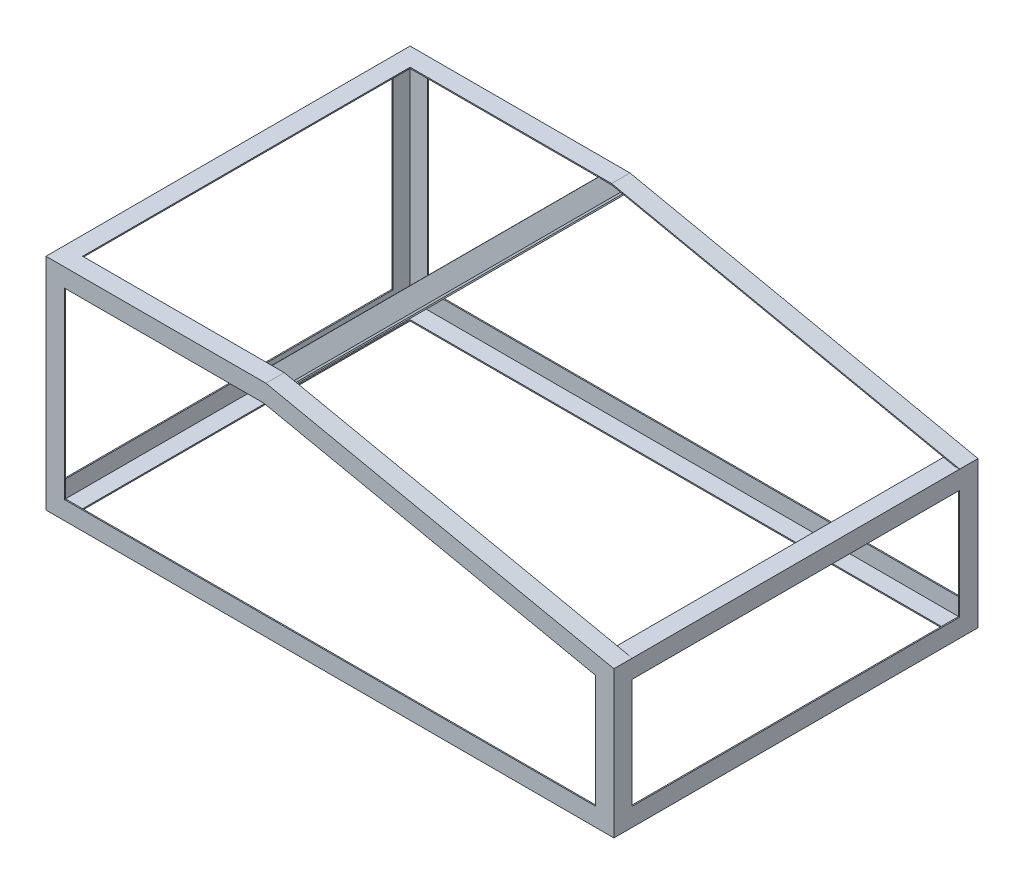
SolidWorks part; units mm, degrees
material "6061 Alloy"
ref_plane "Front Plane" through (0, 0, 0) normal (0, 0, 1) x (1, 0, 0)
ref_plane "Top Plane" through (0, 0, 0) normal (0, 1, 0) x (1, 0, 0)
ref_plane "Right Plane" through (0, 0, 0) normal (1, 0, 0) x (0, 0, -1)
sketch "Sketch2" plane through (0, 0, 0) normal (1, 0, 0) x (0, 0, -1)
  line L0 (-504.825, -346.075) -> (-504.825, -422.275)
  line L1 (504.825, -422.275) -> (-504.825, -422.275) construction
  line L2 (504.825, -422.275) -> (504.825, 422.275) construction
  line L3 (504.825, 422.275) -> (-504.825, 422.275) construction
  line L4 (-504.825, -422.275) -> (-504.825, 422.275) construction
  line L5 (504.825, -422.275) -> (-504.825, 422.275) construction
  line L6 (504.825, 422.275) -> (-504.825, -422.275) construction
  line L7 (-504.825, -422.275) -> (-428.625, -422.275)
  line L8 (-428.625, -422.275) -> (-428.625, -417.195)
  line L9 (-428.625, -417.195) -> (-498.7519, -417.195)
  line L10 (-498.7519, -417.195) -> (-498.7519, -346.075)
  line L11 (-498.7519, -346.075) -> (-504.825, -346.075)
  line L12 (0, 0) -> (0, -148.4726) construction
  line L13 (0, 0) -> (158.633, 0) construction
  line L14 (498.7519, -417.195) -> (498.7519, -346.075)
  line L15 (428.625, -417.195) -> (498.7519, -417.195)
  line L16 (428.625, -422.275) -> (428.625, -417.195)
  line L17 (504.825, -422.275) -> (428.625, -422.275)
  line L18 (504.825, -346.075) -> (504.825, -422.275)
  line L19 (498.7519, -346.075) -> (504.825, -346.075)
  line L20 (428.625, 417.195) -> (498.7519, 417.195)
  line L21 (428.625, 422.275) -> (428.625, 417.195)
  line L22 (504.825, 422.275) -> (428.625, 422.275)
  line L23 (504.825, 346.075) -> (504.825, 422.275)
  line L24 (498.7519, 346.075) -> (504.825, 346.075)
  line L25 (498.7519, 417.195) -> (498.7519, 346.075)
  line L26 (-498.7519, 417.195) -> (-498.7519, 346.075)
  line L27 (-428.625, 417.195) -> (-498.7519, 417.195)
  line L28 (-428.625, 422.275) -> (-428.625, 417.195)
  line L29 (-504.825, 422.275) -> (-428.625, 422.275)
  line L30 (-504.825, 346.075) -> (-504.825, 422.275)
  line L31 (-498.7519, 346.075) -> (-504.825, 346.075)
  point P0 (0, 0)
  dimension "D1" = 1009.65
  dimension "D2" = 844.55
  dimension "D3" = 76.2
  dimension "D4" = 5.08
extrude "OAL Lenth" [suppressed] add sketch "Sketch2" along normal blind 1574.8
sketch "Sketch3" [suppressed] plane through (0, 0, 0) normal (0, 0, 1) x (1, 0, 0)
  line L0 (0, -422.275) -> (0, -346.075)
  line L1 (1574.8, -346.075) -> (0, -346.075) construction
  line L2 (0, -346.075) -> (0, -422.275) construction
  line L3 (0, -346.075) -> (5.08, -346.075)
  line L4 (5.08, -346.075) -> (5.08, -417.195)
  line L5 (5.08, -417.195) -> (76.2, -417.195)
  line L6 (76.2, -417.195) -> (76.2, -422.275)
  line L7 (1574.8, -422.275) -> (0, -422.275) construction
  line L8 (76.2, -422.275) -> (0, -422.275)
  line L9 (0, 0) -> (697.1877, 0) construction
  line L10 (787.4, 346.075) -> (787.4, -346.075) construction
  line L11 (1574.8, 346.075) -> (0, 346.075) construction
  line L12 (76.2, 422.275) -> (0, 422.275)
  line L13 (76.2, 417.195) -> (76.2, 422.275)
  line L14 (5.08, 417.195) -> (76.2, 417.195)
  line L15 (5.08, 346.075) -> (5.08, 417.195)
  line L16 (0, 346.075) -> (5.08, 346.075)
  line L17 (0, 422.275) -> (0, 346.075)
  line L18 (1574.8, 422.275) -> (1574.8, 346.075)
  line L19 (1574.8, 346.075) -> (1569.72, 346.075)
  line L20 (1569.72, 346.075) -> (1569.72, 417.195)
  line L21 (1569.72, 417.195) -> (1498.6, 417.195)
  line L22 (1498.6, 417.195) -> (1498.6, 422.275)
  line L23 (1498.6, 422.275) -> (1574.8, 422.275)
  line L24 (1498.6, -422.275) -> (1574.8, -422.275)
  line L25 (1498.6, -417.195) -> (1498.6, -422.275)
  line L26 (1569.72, -417.195) -> (1498.6, -417.195)
  line L27 (1569.72, -346.075) -> (1569.72, -417.195)
  line L28 (1574.8, -346.075) -> (1569.72, -346.075)
  line L29 (1574.8, -422.275) -> (1574.8, -346.075)
  dimension "D1" = 5.08
extrude "OAL Width" [suppressed] add sketch "Sketch3" along normal up to surface and the other way up to surface
sketch "Sketch4" [suppressed] plane through (0, 422.275, 0) normal (0, 1, 0) x (1, 0, 0)
  line L0 (0, 504.825) -> (0, 428.625)
  line L1 (0, -428.625) -> (0, -504.825) construction
  line L2 (0, 428.625) -> (5.08, 428.625)
  line L3 (5.08, 428.625) -> (5.08, 499.745)
  line L4 (5.08, 499.745) -> (76.2, 499.745)
  line L5 (76.2, 499.745) -> (76.2, 504.825)
  line L6 (0, 504.825) -> (1574.8, 504.825) construction
  line L7 (76.2, 504.825) -> (0, 504.825)
  line L8 (0, 0) -> (1574.8, 0) construction
  line L9 (1574.8, -428.625) -> (1574.8, -504.825) construction
  line L10 (787.4, 0) -> (787.4, 504.825) construction
  line L11 (76.2, -504.825) -> (0, -504.825)
  line L12 (76.2, -499.745) -> (76.2, -504.825)
  line L13 (5.08, -499.745) -> (76.2, -499.745)
  line L14 (5.08, -428.625) -> (5.08, -499.745)
  line L15 (0, -428.625) -> (5.08, -428.625)
  line L16 (0, -504.825) -> (0, -428.625)
  line L17 (1574.8, -504.825) -> (1574.8, -428.625)
  line L18 (1574.8, -428.625) -> (1569.72, -428.625)
  line L19 (1569.72, -428.625) -> (1569.72, -499.745)
  line L20 (1569.72, -499.745) -> (1498.6, -499.745)
  line L21 (1498.6, -499.745) -> (1498.6, -504.825)
  line L22 (1498.6, -504.825) -> (1574.8, -504.825)
  line L23 (1498.6, 504.825) -> (1574.8, 504.825)
  line L24 (1498.6, 499.745) -> (1498.6, 504.825)
  line L25 (1569.72, 499.745) -> (1498.6, 499.745)
  line L26 (1569.72, 428.625) -> (1569.72, 499.745)
  line L27 (1574.8, 428.625) -> (1569.72, 428.625)
  line L28 (1574.8, 504.825) -> (1574.8, 428.625)
  dimension "D1" = 5.08
  dimension "D2" = 76.2
extrude "OAL Height" [suppressed] add sketch "Sketch4" against normal through all
sketch "Sketch5" plane through (0, 0, 0) normal (1, 0, 0) x (0, 0, -1)
  line L0 (0, 304.8) -> (0, -304.8) construction
  line L1 (-504.825, -304.8) -> (504.825, -304.8) construction
  line L2 (-504.825, -304.8) -> (-504.825, -254)
  line L3 (-504.825, -304.8) -> (-454.025, -304.8)
  line L4 (-454.025, -304.8) -> (-454.025, -301.625)
  line L5 (-454.025, -301.625) -> (-501.65, -301.625)
  line L6 (-501.65, -301.625) -> (-501.65, -254)
  line L7 (-501.65, -254) -> (-504.825, -254)
  line L8 (501.65, -254) -> (504.825, -254)
  line L9 (501.65, -301.625) -> (501.65, -254)
  line L10 (454.025, -301.625) -> (501.65, -301.625)
  line L11 (454.025, -304.8) -> (454.025, -301.625)
  line L12 (504.825, -304.8) -> (454.025, -304.8)
  line L13 (504.825, -304.8) -> (504.825, -254)
  point P4 (0, 0)
  point P8 (0, -304.8)
  dimension "D1" = 1009.65
  dimension "D2" = 609.6
  dimension "D3" = 50.8
  dimension "D4" = 3.175
extrude "Bottom Horizontal Angle" add sketch "Sketch5" along normal blind 1574.8 separate body
sketch "Sketch6" plane through (0, -304.8, 0) normal (0, -1, 0) x (1, 0, 0)
  line L0 (965.2, 0) -> (1574.8, 0) construction
  line L1 (1574.8, -504.825) -> (1574.8, 504.825) construction
  line L2 (1574.8, -504.825) -> (1524, -504.825)
  line L3 (1574.8, -504.825) -> (1574.8, -454.025)
  line L4 (1574.8, -454.025) -> (1571.625, -454.025)
  line L5 (1571.625, -454.025) -> (1571.625, -501.65)
  line L6 (1571.625, -501.65) -> (1524, -501.65)
  line L7 (1524, -501.65) -> (1524, -504.825)
  line L8 (1524, 501.65) -> (1524, 504.825)
  line L9 (1571.625, 501.65) -> (1524, 501.65)
  line L10 (1571.625, 454.025) -> (1571.625, 501.65)
  line L11 (1574.8, 454.025) -> (1571.625, 454.025)
  line L12 (1574.8, 504.825) -> (1574.8, 454.025)
  line L13 (1574.8, 504.825) -> (1524, 504.825)
  point P3 (1270, 0)
  point P6 (1574.8, 0)
  dimension "D1" = 50.8
  dimension "D2" = 3.175
  dimension "D3" = 1009.65
extrude "Front Vertial Angle" add sketch "Sketch6" against normal blind 406.4
sketch "Sketch7" plane through (0, -304.8, 0) normal (0, -1, 0) x (1, 0, 0)
  line L0 (609.6, 0) -> (0, 0) construction
  line L1 (0, 504.825) -> (0, -504.825) construction
  line L2 (0, 504.825) -> (50.8, 504.825)
  line L3 (0, 504.825) -> (0, 454.025)
  line L4 (0, 454.025) -> (3.175, 454.025)
  line L5 (3.175, 454.025) -> (3.175, 501.65)
  line L6 (3.175, 501.65) -> (50.8, 501.65)
  line L7 (50.8, 501.65) -> (50.8, 504.825)
  line L8 (50.8, -501.65) -> (50.8, -504.825)
  line L9 (3.175, -501.65) -> (50.8, -501.65)
  line L10 (3.175, -454.025) -> (3.175, -501.65)
  line L11 (0, -454.025) -> (3.175, -454.025)
  line L12 (0, -504.825) -> (0, -454.025)
  line L13 (0, -504.825) -> (50.8, -504.825)
  point P3 (304.8, 0)
  point P6 (0, 0)
extrude "Rear Vertical Angle" add sketch "Sketch7" against normal blind 609.6
sketch "Sketch8" plane through (0, 0, 0) normal (-1, 0, 0) x (0, 0, 1)
  line L0 (0, -304.8) -> (0, 304.8) construction
  line L1 (504.825, 304.8) -> (-504.825, 304.8) construction
  line L2 (504.825, 304.8) -> (504.825, 254)
  line L3 (504.825, 304.8) -> (454.025, 304.8)
  line L4 (454.025, 304.8) -> (454.025, 301.625)
  line L5 (454.025, 301.625) -> (501.65, 301.625)
  line L6 (501.65, 301.625) -> (501.65, 254)
  line L7 (501.65, 254) -> (504.825, 254)
  line L8 (-501.65, 254) -> (-504.825, 254)
  line L9 (-501.65, 301.625) -> (-501.65, 254)
  line L10 (-454.025, 301.625) -> (-501.65, 301.625)
  line L11 (-454.025, 304.8) -> (-454.025, 301.625)
  line L12 (-504.825, 304.8) -> (-454.025, 304.8)
  line L13 (-504.825, 304.8) -> (-504.825, 254)
  point P3 (0, 0)
  point P6 (0, 304.8)
extrude "Rear Top Horizontal Angle" add sketch "Sketch8" against normal blind 609.6
sketch "Sketch9" plane through (0, 0, 504.825) normal (0, 0, 1) x (1, 0, 0)
  line L0 (609.6, 304.8) -> (1574.8, 101.6)
  line L1 (609.6, 304.8) -> (578.7523, 158.2734)
ref_plane "Plane1" through (522.2833, -109.9544, 0) normal (0.9785, -0.206, 0) x (0, 0, -1)
sketch "Sketch10" plane through (522.2833, -109.9544, 0) normal (0.9785, -0.206, 0) x (0, 0, -1)
  line L0 (0, -185.754) -> (0, 423.846) construction
  line L1 (504.825, 423.846) -> (-504.825, 423.846) construction
  line L2 (504.825, 423.846) -> (504.825, 373.046)
  line L3 (504.825, 423.846) -> (454.025, 423.846)
  line L4 (454.025, 423.846) -> (454.025, 420.671)
  line L5 (454.025, 420.671) -> (501.65, 420.671)
  line L6 (501.65, 420.671) -> (501.65, 373.046)
  line L7 (501.65, 373.046) -> (504.825, 373.046)
  line L8 (-501.65, 373.046) -> (-504.825, 373.046)
  line L9 (-501.65, 420.671) -> (-501.65, 373.046)
  line L10 (-454.025, 420.671) -> (-501.65, 420.671)
  line L11 (-454.025, 423.846) -> (-454.025, 420.671)
  line L12 (-504.825, 423.846) -> (-454.025, 423.846)
  line L13 (-504.825, 423.846) -> (-504.825, 373.046)
  point P4 (0, 119.046)
  point P8 (0, 423.846)
  dimension "D1" = 1009.65
  dimension "D2" = 609.6
  dimension "D3" = 50.8
  dimension "D4" = 3.175
extrude "Boss-Extrude5" add sketch "Sketch10" along normal up to vertex
sketch "Sketch11" plane through (0, 0, -504.825) normal (0, 0, -1) x (-1, 0, 0)
  line L0 (0, -101.6) -> (-1574.8, -101.6) construction
  line L1 (-1574.8, 101.6) -> (-1574.8, -304.8) construction
  line L2 (-1574.8, 101.6) -> (-1524, 101.6)
  line L3 (-1574.8, 101.6) -> (-1574.8, 50.8)
  line L4 (-1574.8, 50.8) -> (-1571.625, 50.8)
  line L5 (-1571.625, 50.8) -> (-1571.625, 98.425)
  line L6 (-1571.625, 98.425) -> (-1524, 98.425)
  line L7 (-1524, 98.425) -> (-1524, 101.6)
  line L8 (-1524, -301.625) -> (-1524, -304.8)
  line L9 (-1571.625, -301.625) -> (-1524, -301.625)
  line L10 (-1571.625, -254) -> (-1571.625, -301.625)
  line L11 (-1574.8, -254) -> (-1571.625, -254)
  line L12 (-1574.8, -304.8) -> (-1574.8, -254)
  line L13 (-1574.8, -304.8) -> (-1524, -304.8)
  line L14 (0, -304.8) -> (-50.8, -304.8)
  line L15 (-50.8, -301.625) -> (-50.8, -304.8)
  line L16 (-3.175, -254) -> (-3.175, -301.625)
  line L17 (0, -254) -> (-3.175, -254)
  line L18 (0, -304.8) -> (0, -254)
  line L19 (-3.175, -301.625) -> (-50.8, -301.625)
  line L20 (0, 0) -> (-419.4352, 0) construction
  line L21 (-3.175, 301.625) -> (-50.8, 301.625)
  line L22 (0, 304.8) -> (0, 254)
  line L23 (0, 254) -> (-3.175, 254)
  line L24 (-3.175, 254) -> (-3.175, 301.625)
  line L25 (-50.8, 301.625) -> (-50.8, 304.8)
  line L26 (0, 304.8) -> (-50.8, 304.8)
  line L27 (-605.3402, 263.2815) -> (-644.7354, 295.3543)
  line L28 (-605.3402, 263.2815) -> (-573.2675, 302.6767)
  line L29 (-642.7308, 297.8165) -> (-644.7354, 295.3543)
  line L30 (-605.7978, 267.7483) -> (-642.7308, 297.8165)
  line L31 (-573.2675, 302.6767) -> (-575.7297, 304.6813)
  line L32 (-575.7297, 304.6813) -> (-605.7978, 267.7483)
  line L33 (-643.7056, 301.2489) -> (-575.4944, 308.3511) construction
  line L38 (-643.7056, 301.2489) -> (-643.3359, 297.6977) construction
  line L40 (-575.4944, 308.3511) -> (-575.1246, 304.8) construction
  line L42 (0, 304.8) -> (-609.6, 304.8) construction
  line L43 (-1574.8, 101.6) -> (-609.6, 304.8) construction
  line L44 (-643.3359, 297.6977) -> (-575.1246, 304.8) construction
  line L45 (-609.2302, 301.2489) -> (-606.0734, 270.9299) construction
  line L46 (-642.7977, 298.5481) -> (-575.6628, 303.9496) construction
  line L47 (-609.2302, 301.2489) -> (-605.7978, 267.7483) construction
  point P3 (-787.4, -101.6)
  point P6 (-1574.8, -101.6)
  point P47 (-609.6, 304.8)
  point P51 (-575.4944, 308.3511)
  dimension "D1" = 50.8
  dimension "D2" = 3.175
  dimension "D3" = 68.58
extrude "Boss-Extrude6" add sketch "Sketch11" against normal through all
